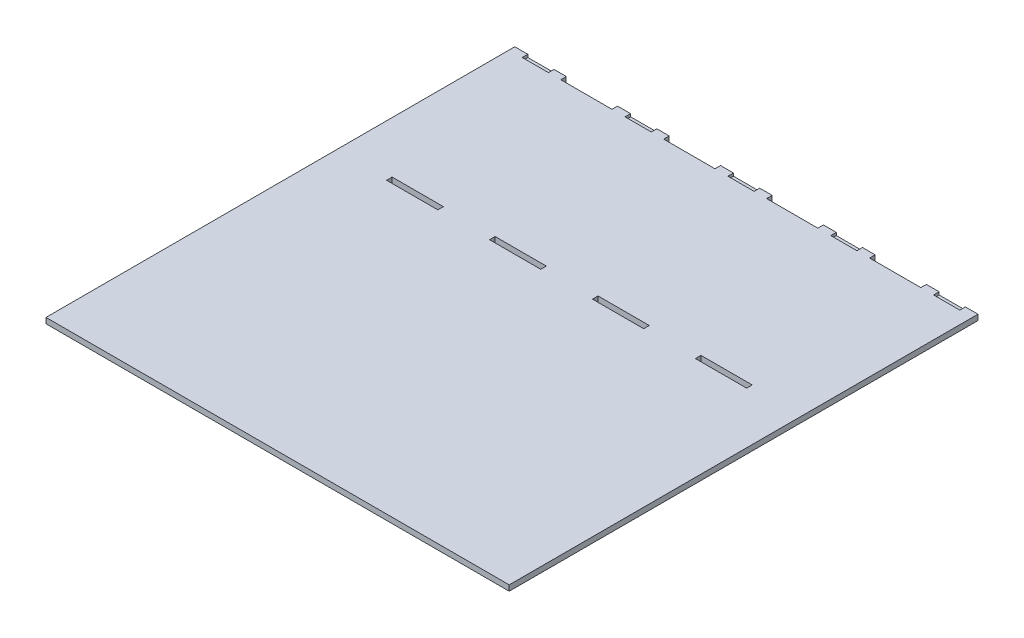
SolidWorks part; units mm, degrees
material "Pine"
ref_plane "Front Plane" through (0, 0, 0) normal (0, 0, 1) x (1, 0, 0)
ref_plane "Top Plane" through (0, 0, 0) normal (0, 1, 0) x (1, 0, 0)
ref_plane "Right Plane" through (0, 0, 0) normal (1, 0, 0) x (0, 0, -1)
sketch "Sketch2" plane through (0, 0, 0) normal (0, 1, 0) x (1, 0, 0)
  line L1 (-250, -253) -> (250, -253)
  line L2 (-250, -253) -> (-250, 253)
  line L3 (-250, 253) -> (250, 253)
  line L4 (250, -253) -> (250, 253)
  line L5 (-250, -253) -> (250, 253) construction
  line L6 (-250, 253) -> (250, -253) construction
  point P0 (0, 0)
  dimension "D1" = 500
  dimension "D2" = 506
extrude "Boss-Extrude1" add sketch "Sketch2" along normal blind 6
sketch "Sketch3" plane through (0, 6, 0) normal (0, 1, 0) x (1, 0, 0)
  line L0 (250, 253) -> (-250, 253) construction
  line L1 (194.4, 253) -> (138.8, 253)
  line L2 (194.4, 253) -> (194.4, 247)
  line L3 (194.4, 247) -> (138.8, 247)
  line L4 (138.8, 253) -> (138.8, 247)
  line L5 (250, -253) -> (250, 253) construction
  ellipse E0 centre (194.4, 250) end of major axis (194.4, 247) minor radius 0.2
  ellipse E1 centre (138.8, 250) end of major axis (138.8, 247) minor radius 0.2
  line M6 (250, 253) -> (-250, 253)
  dimension "D1" = 6
  dimension "D2" = 55.6
  dimension "D3" = 55.6
  dimension "D4" = 0.2
  dimension "D5" = 0.2
extrude "Cut-Extrude1" cut sketch "Sketch3" against normal blind 6 contours E1 L3 E0 M6
pattern_linear "LPattern1" count 4 spacing 111.1 along (-1, 0, 0) of "Cut-Extrude1"
pattern_linear "LPattern2" count 2 spacing 188 along (0, 0, -1) of "Cut-Extrude1"
pattern_linear "LPattern3" count 4 spacing 111.1 along (1, 0, 0) of "LPattern2"
sketch "Sketch8" plane through (0, 6, 0) normal (0, 1, 0) x (1, 0, 0)
  line L0 (250, 247) -> (-250, 247)
  line L1 (250, -253) -> (250, 253) construction
  line L2 (-250, 253) -> (-250, -253) construction
  line L3 (250, 253) -> (194.4, 253) construction
  dimension "D1" = 6
sketch "Sketch9" plane through (0, 6, 0) normal (0, 1, 0) x (1, 0, 0)
  line L0 (250, 253) -> (194.4, 253) construction
  line L1 (208.05, 247) -> (236.35, 247)
  line L2 (208.05, 247) -> (208.05, 253)
  line L3 (208.05, 253) -> (236.35, 253)
  line L4 (236.35, 247) -> (236.35, 253)
  dimension "D1" = 6
  dimension "D2" = 13.65
  dimension "D3" = 13.65
extrude "Cut-Extrude3" cut sketch "Sketch9" against normal blind 3
pattern_linear "LPattern5" count 5 spacing 111 along (-1, 0, 0) of "Cut-Extrude3"
